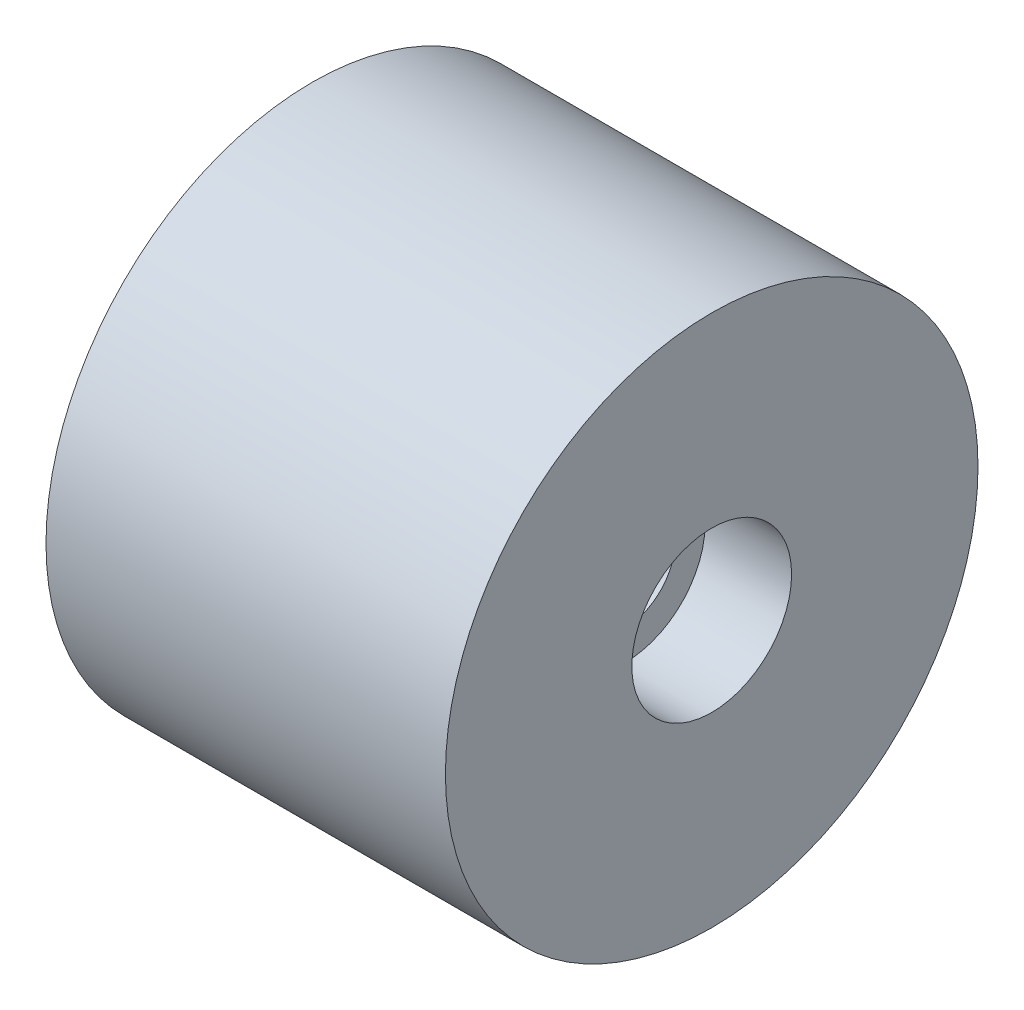
SolidWorks part; units mm, degrees
ref_plane "Front Plane" through (0, 0, 0) normal (0, 0, 1) x (1, 0, 0)
ref_plane "Top Plane" through (0, 0, 0) normal (0, 1, 0) x (1, 0, 0)
ref_plane "Right Plane" through (0, 0, 0) normal (1, 0, 0) x (0, 0, -1)
sketch "Sketch1" plane through (0, 0, 0) normal (1, 0, 0) x (0, 0, -1)
  circle A0 centre (0, 0) radius 8
  dimension "D1" = 16
extrude "Boss-Extrude1" add sketch "Sketch1" along normal blind 12
sketch "Sketch2" plane through (0, 0, 0) normal (-1, 0, 0) x (0, 0, 1)
  line L1 (6.4663, 0) -> (3.2332, 5.6)
  line L2 (3.2332, 5.6) -> (-3.2332, 5.6)
  line L3 (-3.2332, 5.6) -> (-6.4663, 0)
  line L4 (-6.4663, 0) -> (-3.2332, -5.6)
  line L5 (-3.2332, -5.6) -> (3.2332, -5.6)
  line L6 (3.2332, -5.6) -> (6.4663, 0)
  circle A0 centre (0, 0) radius 5.6 construction
  dimension "D1" = 11.2
extrude "Cut-Extrude1" cut sketch "Sketch2" against normal blind 6
sketch "Sketch3" plane through (12, 0, 0) normal (1, 0, 0) x (0, 0, -1)
  circle A0 centre (0, 0) radius 2.4
  dimension "D1" = 4.8
extrude "Cut-Extrude2" cut sketch "Sketch3" against normal blind 2.6
sketch "Sketch4" plane through (9.4, 0, 0) normal (1, 0, 0) x (0, 0, -1)
  circle A0 centre (0, 0) radius 1.5
  dimension "D1" = 3
extrude "Cut-Extrude3" cut sketch "Sketch4" against normal through all
sketch "Sketch5" plane through (6, 0, 0) normal (-1, 0, 0) x (0, 0, 1)
  circle A0 centre (0, 0) radius 3
  dimension "D1" = 6
extrude "Cut-Extrude4" cut sketch "Sketch5" against normal blind 2
